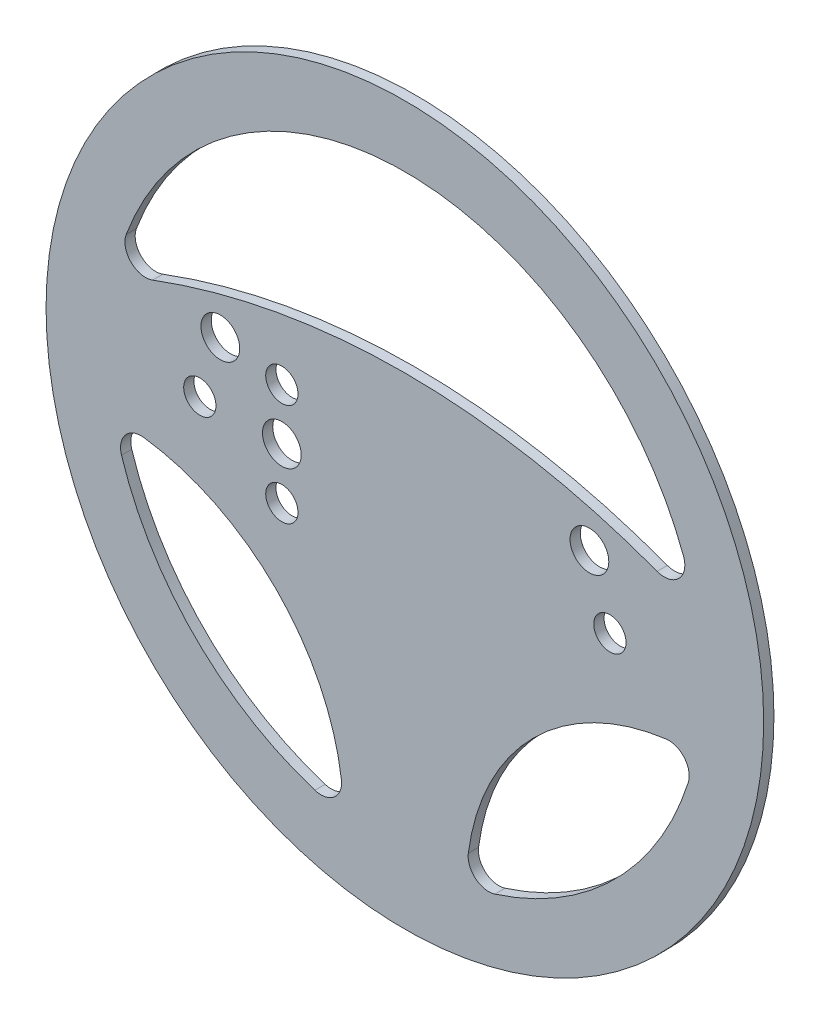
SolidWorks part; units mm, degrees
ref_plane "Front Plane" through (0, 0, 0) normal (0, 0, 1) x (1, 0, 0)
ref_plane "Top Plane" through (0, 0, 0) normal (0, 1, 0) x (1, 0, 0)
ref_plane "Right Plane" through (0, 0, 0) normal (1, 0, 0) x (0, 0, -1)
sketch "Sketch1" plane through (0, 0, 0) normal (0, 0, 1) x (1, 0, 0)
  line L0 (132.4963, 0) -> (-132.4963, 0) construction
  line L1 (0, -179.0618) -> (0, 179.0618) construction
  line L2 (-19.05, -90.0828) -> (19.05, -90.0828) construction
  line L3 (-90.0828, -19.05) -> (-90.0828, 19.05) construction
  line L4 (90.0828, -19.05) -> (90.0828, 19.05) construction
  circle A0 centre (0, 0) radius 111.125
  circle A1 centre (0, 0) radius 92.075 construction
  arc A2 (-78.1188, 23.9365) -> (78.1188, 23.9365) centre (0, -184.4146) cw
  arc A3 (-86.2998, 32.0959) -> (86.2998, 32.0959) centre (0, 0) cw
  arc A4 (19.6484, -80.8821) -> (80.8821, -19.6484) centre (90.0828, -90.0828) cw
  arc A5 (-19.6484, -80.8821) -> (-80.8821, -19.6484) centre (-90.0828, -90.0828) ccw
  arc A6 (-87.7568, -27.8667) -> (-27.8667, -87.7568) centre (0, 0) ccw
  arc A7 (27.8667, -87.7568) -> (87.7568, -27.8667) centre (0, 0) ccw
  arc A8 (27.8667, -87.7568) -> (19.6484, -80.8821) centre (25.9449, -81.7046) cw
  arc A9 (80.8821, -19.6484) -> (87.7568, -27.8667) centre (81.7046, -25.9449) cw
  arc A10 (78.1188, 23.9365) -> (86.2998, 32.0959) centre (80.3481, 29.8824) ccw
  arc A11 (-78.1188, 23.9365) -> (-86.2998, 32.0959) centre (-80.3481, 29.8824) cw
  arc A12 (-27.8667, -87.7568) -> (-19.6484, -80.8821) centre (-25.9449, -81.7046) ccw
  arc A13 (-87.7568, -27.8667) -> (-80.8821, -19.6484) centre (-81.7046, -25.9449) cw
  point P6 (0, 0)
  point P10 (0, 0)
  point P13 (0, -90.0828)
  point P16 (-90.0828, 0)
  point P19 (90.0828, 0)
  point P21 (0, 38.1)
  dimension "D1" = 222.25
  dimension "D2" = 184.15
  dimension "D5" = 6.35
  dimension "D3" = 38.1
  dimension "D4" = 38.1
extrude "Boss-Extrude1" add sketch "Sketch1" along normal blind 3.175
sketch "Sketch2" plane through (0, 0, 0) normal (0, 0, -1) x (-1, 0, 0)
  line L0 (0, -143.7345) -> (0, 143.7345) construction
  line L1 (284.4599, 0) -> (-284.4599, 0) construction
  circle A0 centre (-57.15, 19.05) radius 6
  circle A1 centre (-63.5, 0) radius 5
  circle A2 centre (57.15, 19.05) radius 6
  circle A3 centre (63.5, 0) radius 5
  circle A4 centre (38.1, 0) radius 6
  circle A5 centre (38.1, 15.875) radius 5
  circle A6 centre (38.1, -15.875) radius 5
  point P6 (0, 0)
  point P11 (0, 0)
  point P19 (42.8238, 0)
  point P22 (0, 0)
  point P23 (0, 0)
  dimension "D1" = 12
  dimension "D4" = 10
  dimension "D5" = 63.5
  dimension "D6" = 15.875
  dimension "D2" = 57.15
  dimension "D3" = 19.05
  dimension "D7" = 15.875
  dimension "D8" = 38.1
extrude "Cut-Extrude1" cut sketch "Sketch2" against normal up to surface (3.175 mm away) up to face at (111.125, 0, 3.175)
